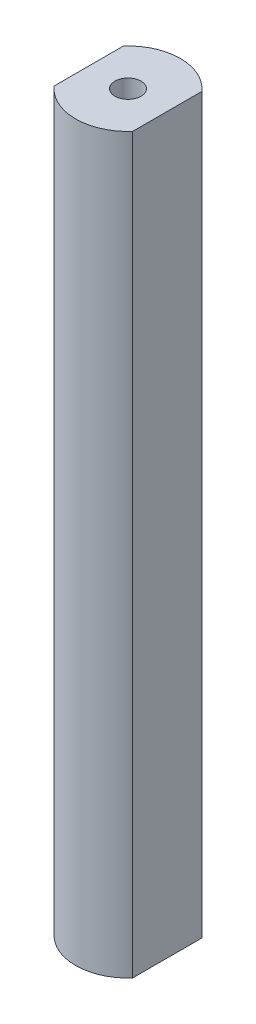
SolidWorks part; units mm, degrees
ref_plane "Front Plane" through (0, 0, 0) normal (0, 0, 1) x (1, 0, 0)
ref_plane "Top Plane" through (0, 0, 0) normal (0, 1, 0) x (1, 0, 0)
ref_plane "Right Plane" through (0, 0, 0) normal (1, 0, 0) x (0, 0, -1)
sketch "Sketch1" plane through (0, 0, 0) normal (0, 1, 0) x (1, 0, 0)
  circle A0 centre (0, 0) radius 6.35
  circle A1 centre (0, 0) radius 1.5875
  dimension "D1" = 12.7
  dimension "D2" = 3.175
extrude "Boss-Extrude1" add sketch "Sketch1" along normal blind 88.9
sketch "Sketch2" plane through (0, 88.9, 0) normal (0, 1, 0) x (1, 0, 0)
  line L1 (-4.7625, -11.0607) -> (4.7625, -11.0607)
  line L2 (-4.7625, -11.0607) -> (-4.7625, 11.0607)
  line L3 (-4.7625, 11.0607) -> (4.7625, 11.0607)
  line L4 (4.7625, -11.0607) -> (4.7625, 11.0607)
  line L5 (-4.7625, -11.0607) -> (4.7625, 11.0607) construction
  line L6 (-4.7625, 11.0607) -> (4.7625, -11.0607) construction
  circle A1 centre (0, 0) radius 6.35
  circle A2 centre (0, 0) radius 6.35
  point P0 (0, 0)
  circle M6 centre (0, 0) radius 6.35
  dimension "D1" = 9.525
  dimension "D2" = 0
extrude "Cut-Extrude1" cut sketch "Sketch2" against normal through all contours L2 M6 | L4 M6
